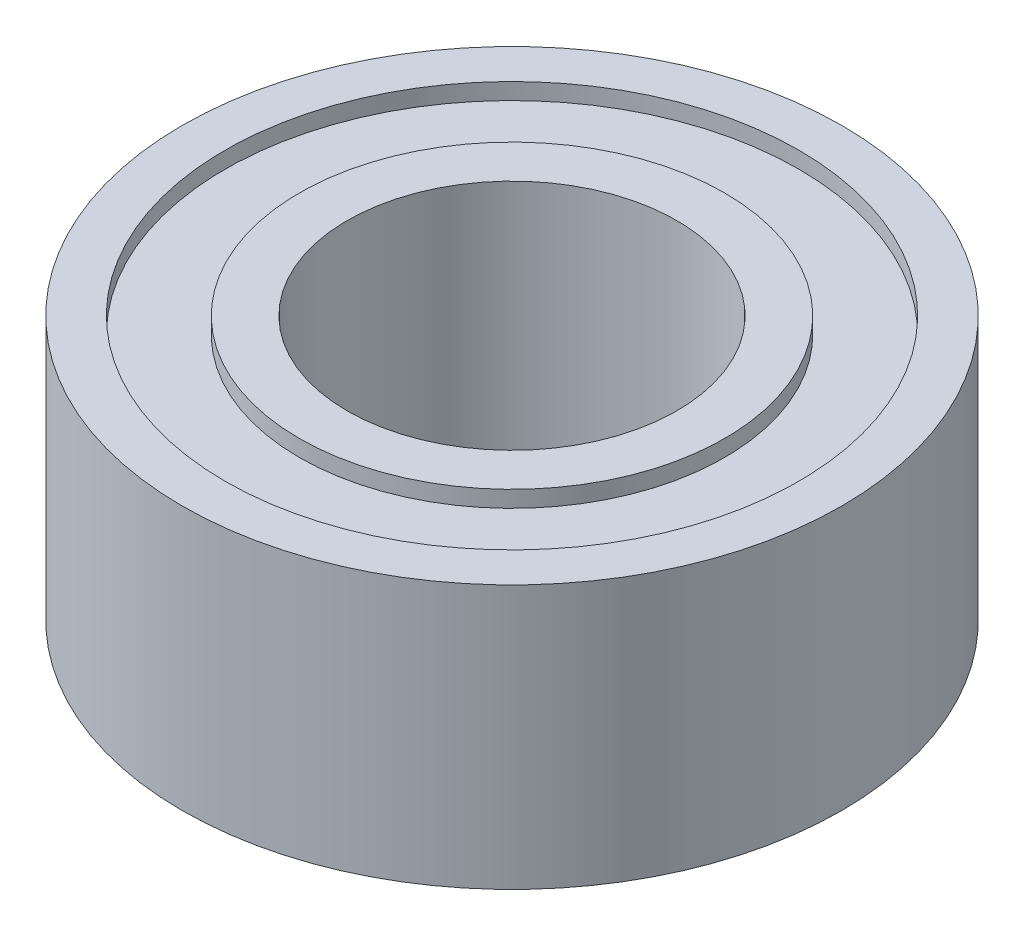
SolidWorks part; units mm, degrees
ref_plane "Front Plane" through (0, 0, 0) normal (0, 0, 1) x (1, 0, 0)
ref_plane "Top Plane" through (0, 0, 0) normal (0, 1, 0) x (1, 0, 0)
ref_plane "Right Plane" through (0, 0, 0) normal (1, 0, 0) x (0, 0, -1)
sketch "Sketch1" plane through (0, 0, 0) normal (0, 1, 0) x (1, 0, 0)
  circle A0 centre (0, 0) radius 5
  circle A1 centre (0, 0) radius 2.5
  dimension "D1" = 10
  dimension "D2" = 5
extrude "Boss-Extrude1" add sketch "Sketch1" along normal blind 4
sketch "Sketch2" plane through (0, 4, 0) normal (0, 1, 0) x (1, 0, 0)
  circle A0 centre (0, 0) radius 4.35
  circle A1 centre (0, 0) radius 3.225
  dimension "D1" = 8.7
  dimension "D2" = 6.45
extrude "Cut-Extrude1" cut sketch "Sketch2" against normal blind 0.25
sketch "Sketch3" plane through (0, 0, 0) normal (0, -1, 0) x (1, 0, 0)
  circle A0 centre (0, 0) radius 4.35
  circle A1 centre (0, 0) radius 3.225
  circle A2 centre (0, 0) radius 4.35 construction
  circle A3 centre (0, 0) radius 3.225 construction
extrude "Cut-Extrude2" cut sketch "Sketch3" against normal blind 0.25
